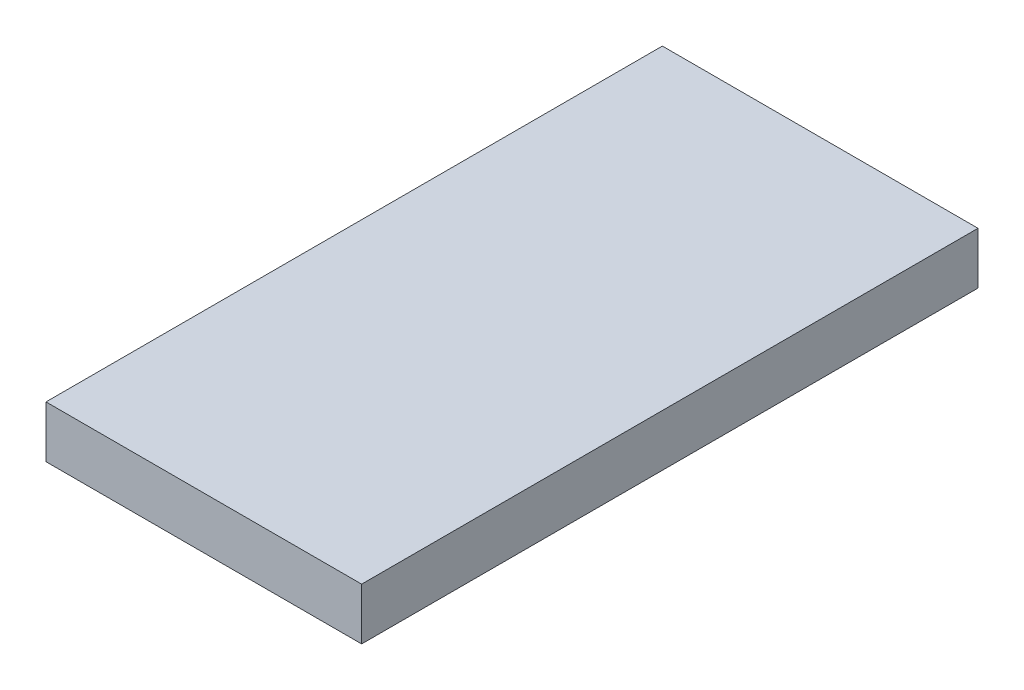
SolidWorks part; units mm, degrees
ref_plane "Front Plane" through (0, 0, 0) normal (0, 0, 1) x (1, 0, 0)
ref_plane "Top Plane" through (0, 0, 0) normal (0, 1, 0) x (1, 0, 0)
ref_plane "Right Plane" through (0, 0, 0) normal (1, 0, 0) x (0, 0, -1)
sketch "Sketch1" plane through (0, 0, 0) normal (0, 1, 0) x (1, 0, 0)
  line L1 (0, 0) -> (66.04, 0)
  line L2 (0, 0) -> (0, 128.96)
  line L3 (0, 128.96) -> (66.04, 128.96)
  line L4 (66.04, 0) -> (66.04, 128.96)
extrude "Boss-Extrude1" add sketch "Sketch1" along normal blind 10.84
